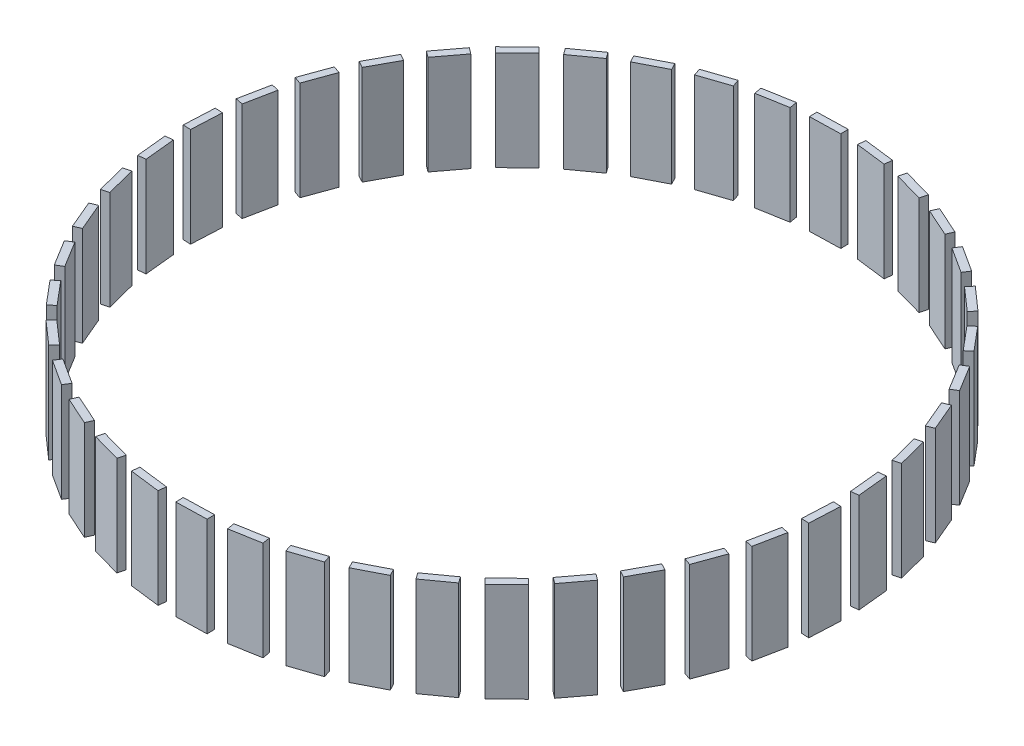
SolidWorks part; units mm, degrees
material "1060 Alloy"
ref_plane "Front Plane" through (0, 0, 0) normal (0, 0, 1) x (1, 0, 0)
ref_plane "Top Plane" through (0, 0, 0) normal (0, 1, 0) x (1, 0, 0)
ref_plane "Right Plane" through (0, 0, 0) normal (1, 0, 0) x (0, 0, -1)
sketch "Sketch2" plane through (54.6393, 0, -23.0985) normal (-0.9211, 0, 0.3894) x (0.3894, 0, 0.9211)
  line L0 (84.5038, 43.1819) -> (84.5038, 51.1819) construction
  line L1 (80.5038, 57.1819) -> (84.5038, 57.1819)
  line L2 (80.5038, 57.1819) -> (80.5038, 44.1819)
  line L3 (80.5038, 44.1819) -> (84.5038, 44.1819)
  line L4 (84.5038, 57.1819) -> (84.5038, 44.1819)
  dimension "D1" = 13
extrude "Boss-Extrude1" add sketch "Sketch2" along normal blind 1
pattern_circular "CirPattern1" count 42 over 360 about axis through (47.0847, 0, 69.6683) along (0, 1, 0) of bodies 101
sketch "Sketch3" plane through (0, 44.1819, 0) normal (0, -1, 0) x (1, 0, 0)
  line L0 (48.2029, 112.7338) -> (45.9664, 26.6028) construction
  line L1 (50.2022, 112.6819) -> (46.2036, 112.7857) construction
  line L2 (43.9671, 26.6547) -> (47.9658, 26.5509) construction
  line L3 (4.056, 67.5651) -> (90.1133, 71.7715)
  line L4 (3.9584, 69.5627) -> (4.1537, 65.5675) construction
  line L5 (90.2109, 69.7739) -> (90.0157, 73.7691) construction
  line L6 (5.3477, 80.3415) -> (88.8216, 58.9952)
  line L7 (5.8432, 82.2791) -> (4.8522, 78.4038) construction
  line L8 (88.3261, 57.0575) -> (89.3171, 60.9328) construction
  circle A0 centre (47.0847, 69.6683) radius 43.08
ref_plane "Plane1" through (-16.3931, 0, 21.6882) normal (-0.603, 0, 0.7978) x (0.7978, 0, 0.603)
